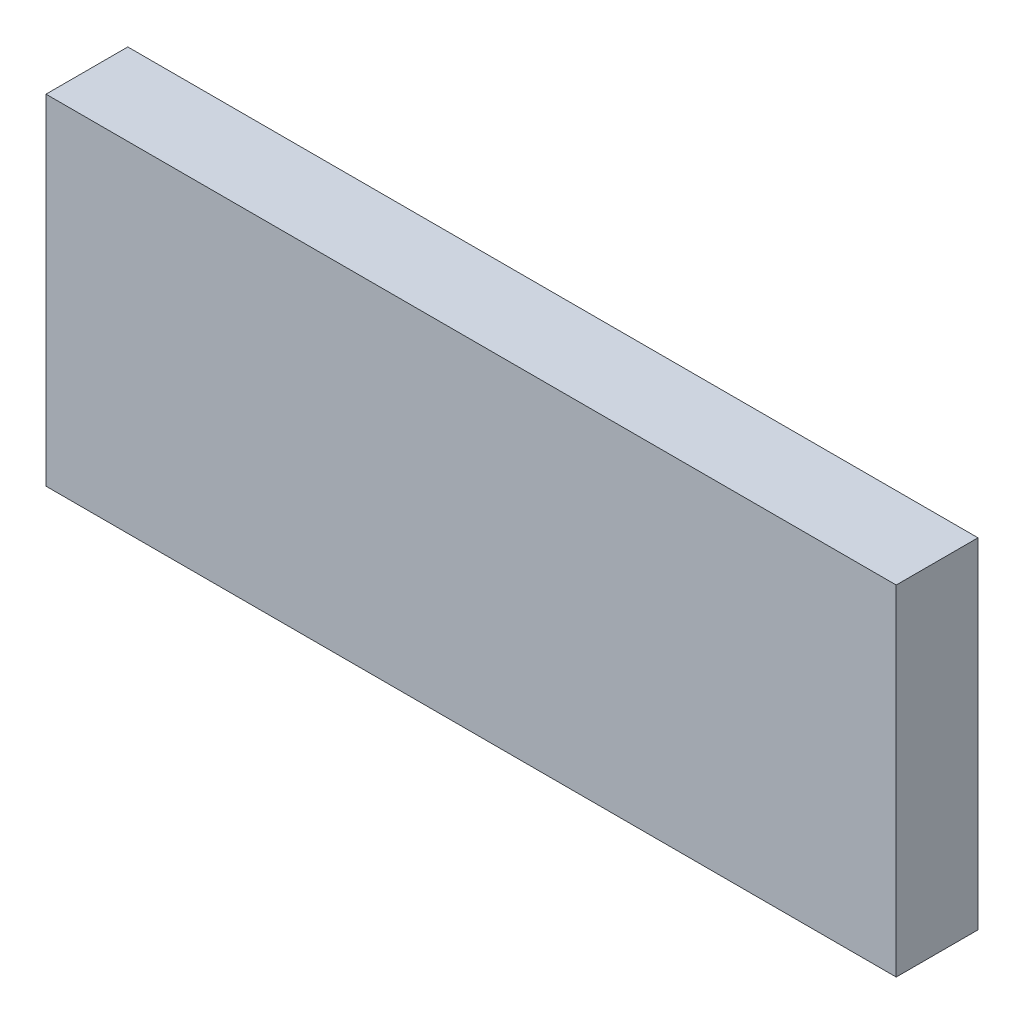
SolidWorks part; units mm, degrees
ref_plane "Front Plane" through (0, 0, 0) normal (0, 0, 1) x (1, 0, 0)
ref_plane "Top Plane" through (0, 0, 0) normal (0, 1, 0) x (1, 0, 0)
ref_plane "Right Plane" through (0, 0, 0) normal (1, 0, 0) x (0, 0, -1)
other "Configuration Table"
sketch "Sketch1" plane through (0, 0, 0) normal (0, 1, 0) x (1, 0, 0)
  line L1 (0, 0) -> (67.564, 0)
  line L2 (0, 0) -> (0, -6.4999)
  line L3 (0, -6.4999) -> (67.564, -6.4999)
  line L4 (67.564, 0) -> (67.564, -6.4999)
  dimension "D1" = 67.564
  dimension "D2" = 6.4999
extrude "Boss-Extrude1" add sketch "Sketch1" along normal blind 26.9824
